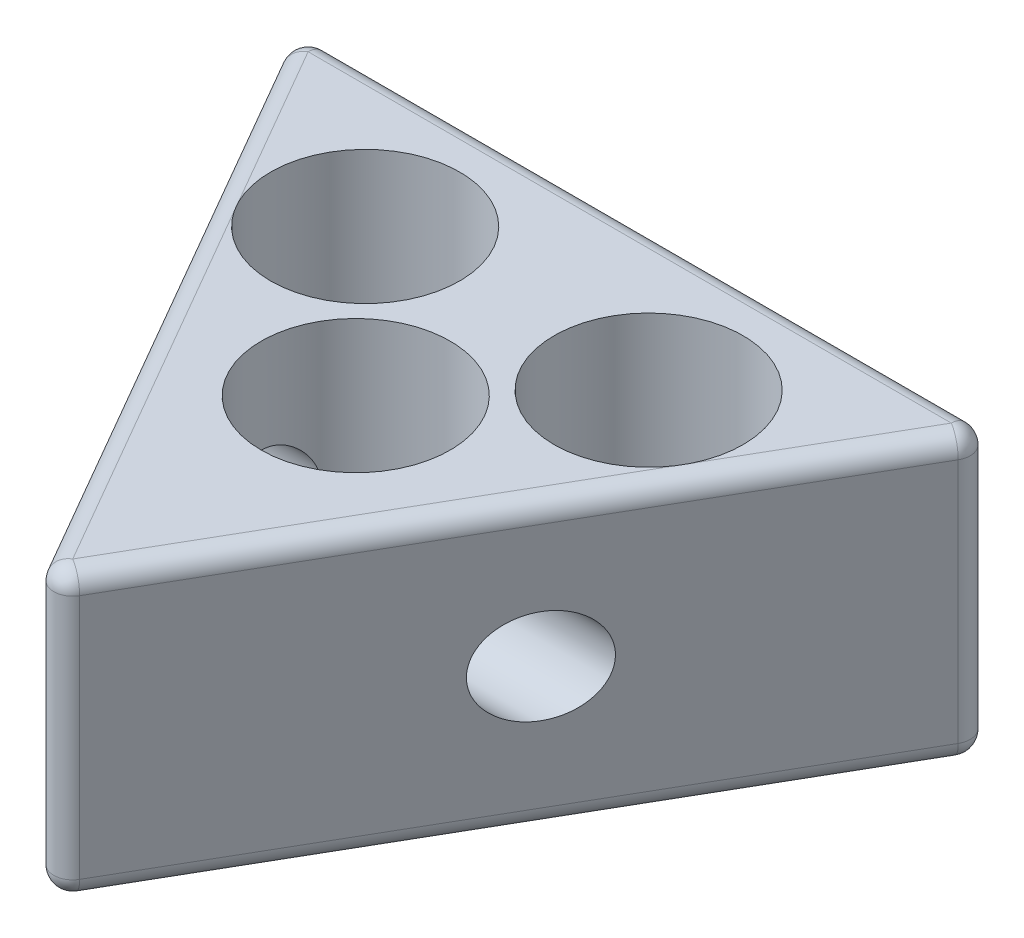
SolidWorks part; units mm, degrees
ref_plane "Front Plane" through (0, 0, 0) normal (0, 0, 1) x (1, 0, 0)
ref_plane "Top Plane" through (0, 0, 0) normal (0, 1, 0) x (1, 0, 0)
ref_plane "Right Plane" through (0, 0, 0) normal (1, 0, 0) x (0, 0, -1)
sketch "Sketch1" plane through (0, 0, 0) normal (0, 1, 0) x (1, 0, 0)
  line L0 (0, 0) -> (37.5, 64.9519)
  line L1 (37.5, 64.9519) -> (-37.5, 64.9519)
  line L2 (-37.5, 64.9519) -> (0, 0)
  dimension "D1" = 75
extrude "Boss-Extrude1" add sketch "Sketch1" along normal blind 30
sketch "Sketch2" plane through (0, 30, 0) normal (0, 1, 0) x (1, 0, 0)
  line L0 (37.5, 64.9519) -> (-37.5, 64.9519) construction
  line L1 (-15, 49.9519) -> (15, 49.9519) construction
  circle A0 centre (-15, 49.9519) radius 10
  circle A1 centre (15, 49.9519) radius 10
  circle A2 centre (0, 33.9519) radius 10
  point P4 (0, 49.9519)
  point P5 (0, 0)
  point P10 (0, 0)
  dimension "D1" = 20
  dimension "D4" = 20
  dimension "D2" = 15
  dimension "D3" = 15
  dimension "D5" = 16
fillet "Fillet1" radius 2 9 edges at (0, 30, -64.9519) (0, 0, -64.9519) (18.75, 0, -32.476) (-18.75, 0, -32.476) (-18.75, 30, -32.476) (18.75, 30, -32.476) (0, 15, 0) (37.5, 15, -64.9519) (-37.5, 15, -64.9519)
ref_plane "Plane1" through (-36.0359, 0, 0) normal (-1, 0, 0) x (0, 0, 1)
sketch "Sketch3" plane through (-36.0359, 0, 0) normal (-1, 0, 0) x (0, 0, 1)
  line L1 (-3, 2) -> (-3, 28) construction
  circle A0 centre (-33.9519, 15) radius 5
  point P2 (0, 0)
  point P3 (0, 0)
  point P6 (0, 0)
  point P9 (-3, 15)
  point P10 (0, 0)
  dimension "D1" = 10
extrude "Cut-Extrude3" cut sketch "Sketch2" against normal through all
extrude "Cut-Extrude4" cut sketch "Sketch3" against normal through all contours A0
